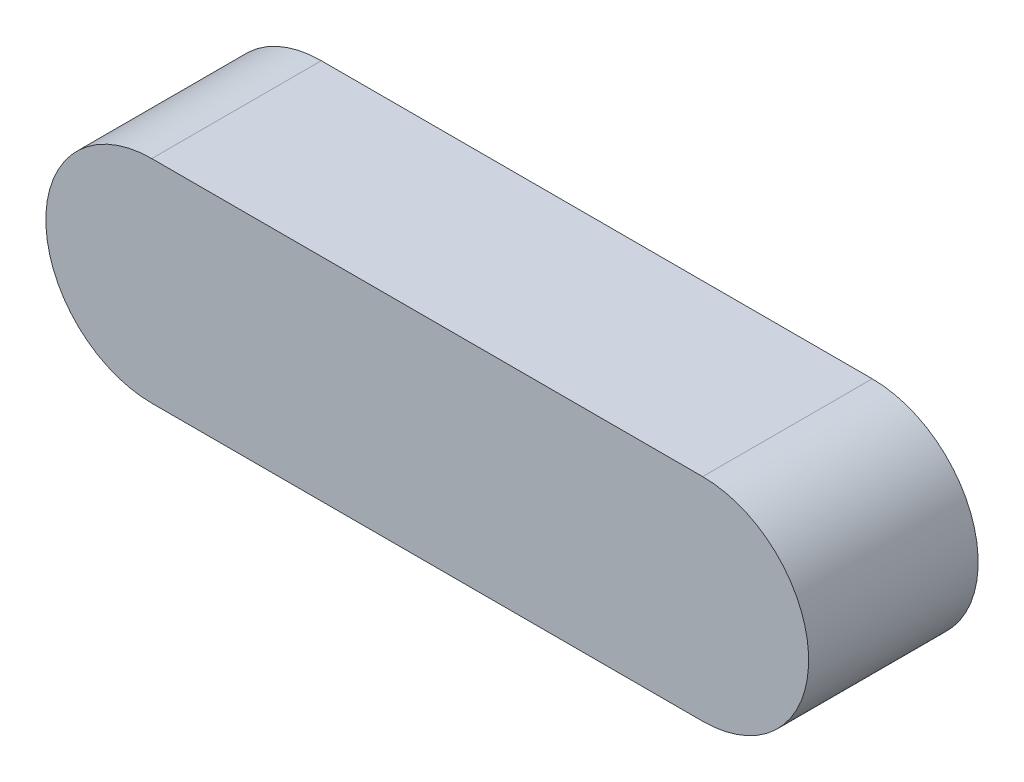
SolidWorks part; units mm, degrees
ref_plane "Front Plane" through (0, 0, 0) normal (0, 0, 1) x (1, 0, 0)
ref_plane "Top Plane" through (0, 0, 0) normal (0, 1, 0) x (1, 0, 0)
ref_plane "Right Plane" through (0, 0, 0) normal (1, 0, 0) x (0, 0, -1)
sketch "Sketch1" plane through (0, 0, 0) normal (0, 0, 1) x (1, 0, 0)
  line L0 (-5.415, 0) -> (20.585, 0) construction
  line L1 (-5.415, 5) -> (20.585, 5)
  line L2 (-5.415, -5) -> (20.585, -5)
  arc A0 (-5.415, 5) -> (-5.415, -5) centre (-5.415, 0) ccw
  arc A1 (20.585, -5) -> (20.585, 5) centre (20.585, 0) ccw
  point P3 (7.585, 0)
  dimension "D1" = 5
  dimension "D2" = 26
extrude "Boss-Extrude1" add sketch "Sketch1" along normal blind 8
